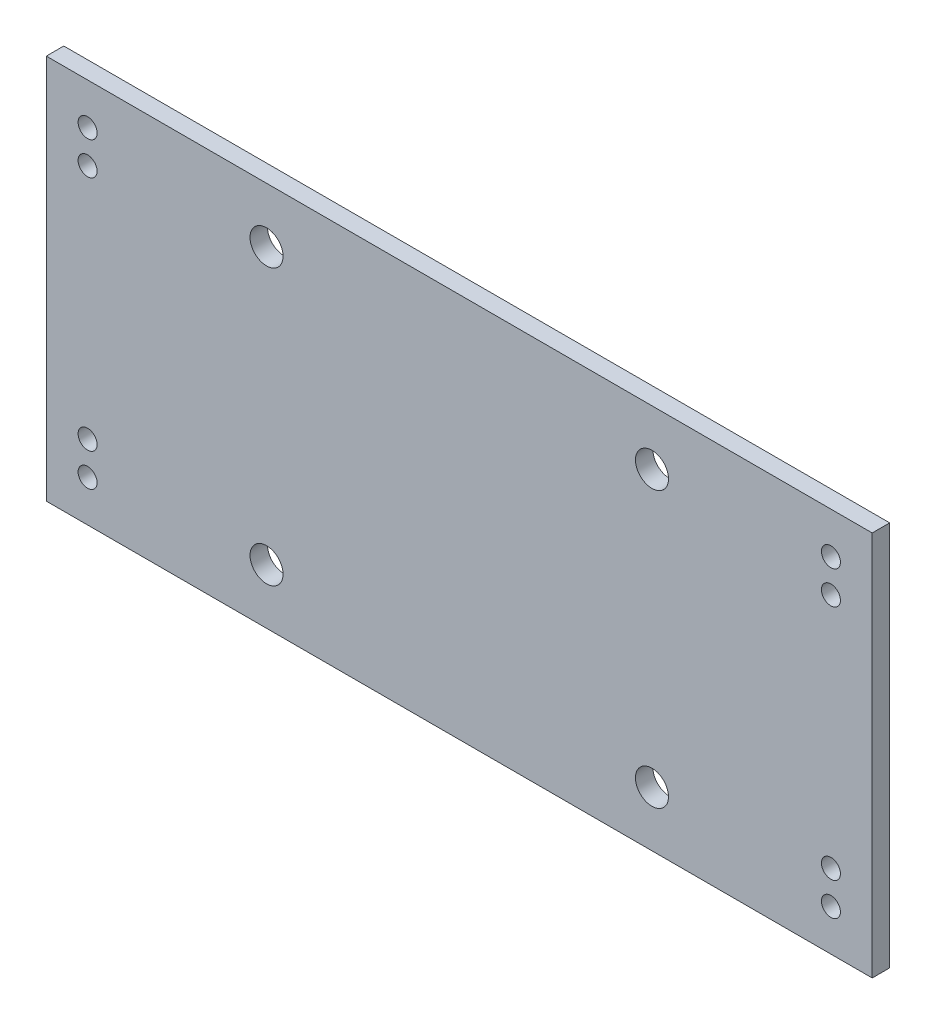
SolidWorks part; units mm, degrees
ref_plane "Front Plane" through (0, 0, 0) normal (0, 0, 1) x (1, 0, 0)
ref_plane "Top Plane" through (0, 0, 0) normal (0, 1, 0) x (1, 0, 0)
ref_plane "Right Plane" through (0, 0, 0) normal (1, 0, 0) x (0, 0, -1)
sketch "Sketch1" plane through (0, 0, 0) normal (0, 0, 1) x (1, 0, 0)
  line L1 (0, 0) -> (150, 0)
  line L2 (0, 0) -> (0, -70)
  line L3 (0, -70) -> (150, -70)
  line L4 (150, 0) -> (150, -70)
  line L5 (7.5, -7.5) -> (142.5, -7.5) construction
  line L6 (7.5, -7.5) -> (7.5, -62.5) construction
  line L7 (7.5, -62.5) -> (142.5, -62.5) construction
  line L8 (142.5, -7.5) -> (142.5, -62.5) construction
  line L9 (7.5, -13.5) -> (142.5, -13.5) construction
  line L10 (7.5, -13.5) -> (7.5, -56.5) construction
  line L11 (7.5, -56.5) -> (142.5, -56.5) construction
  line L12 (142.5, -13.5) -> (142.5, -56.5) construction
  line L13 (40, -10) -> (110, -10) construction
  line L14 (40, -10) -> (40, -60) construction
  line L15 (40, -60) -> (110, -60) construction
  line L16 (110, -10) -> (110, -60) construction
  circle A0 centre (7.5, -7.5) radius 1.725
  circle A1 centre (142.5, -7.5) radius 1.725
  circle A2 centre (142.5, -62.5) radius 1.725
  circle A3 centre (7.5, -62.5) radius 1.725
  circle A4 centre (7.5, -13.5) radius 1.725
  circle A5 centre (142.5, -13.5) radius 1.725
  circle A6 centre (142.5, -56.5) radius 1.725
  circle A7 centre (7.5, -56.5) radius 1.725
  circle A8 centre (40, -10) radius 3
  circle A9 centre (40, -60) radius 3
  circle A10 centre (110, -10) radius 3
  circle A11 centre (110, -60) radius 3
  point P29 (22.9758, -11.6045)
  dimension "D1" = 3.45
  dimension "D12" = 6
  dimension "D2" = 135
  dimension "D3" = 55
  dimension "D4" = 150
  dimension "D5" = 7.5
  dimension "D6" = 43
  dimension "D7" = 6
  dimension "D8" = 70
  dimension "D9" = 7.5
  dimension "D10" = 50
  dimension "D11" = 10
  dimension "D13" = 70
  dimension "D14" = 40
extrude "Boss-Extrude1" add sketch "Sketch1" along normal blind 3.175 contours L4 L1 L2 L3 A7 L10 A4 L9 A5 L12 A6 L11 A3 A2 A1 A0
equation "\"D5@Sketch1\"=(\"D4@Sketch1\"-\"D2@Sketch1\")/2"
equation "\"D9@Sketch1\"= (\"D8@Sketch1\"-\"D3@Sketch1\")/2"
equation "\"D11@Sketch1\"=(\"D8@Sketch1\"-\"D10@Sketch1\")/2"
equation "\"D14@Sketch1\"=(\"D4@Sketch1\"-\"D13@Sketch1\")/2"
